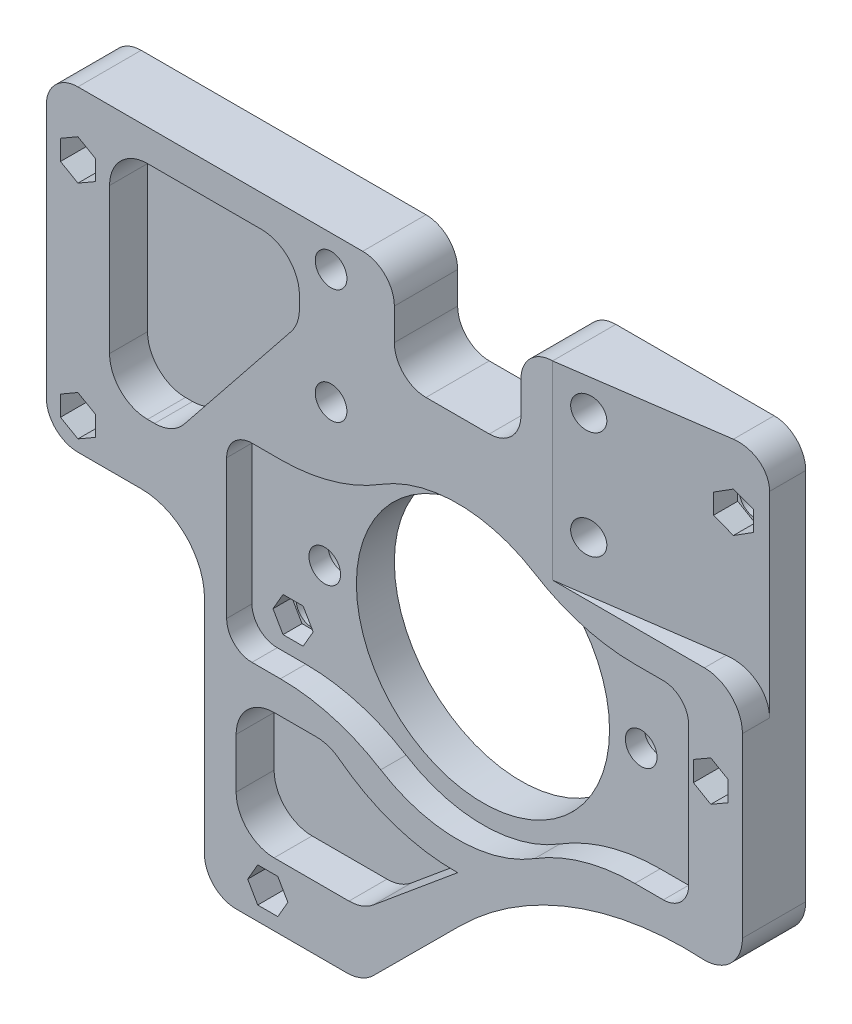
SolidWorks part; units mm, degrees
ref_plane "Front Plane" through (0, 0, 0) normal (0, 0, 1) x (1, 0, 0)
ref_plane "Top Plane" through (0, 0, 0) normal (0, 1, 0) x (1, 0, 0)
ref_plane "Right Plane" through (0, 0, 0) normal (1, 0, 0) x (0, 0, -1)
sketch "Sketch1" plane through (0, 0, 0) normal (0, 0, 1) x (1, 0, 0)
  line L0 (0, 5) -> (0, 40)
  line L1 (-10, 50) -> (-20, 50)
  line L2 (-25, 55) -> (-25, 95)
  line L3 (-20, 100) -> (25, 100)
  line L4 (30, 95) -> (30, 90)
  line L5 (35, 85) -> (45, 85)
  line L6 (50, 90) -> (50, 95)
  line L7 (55, 100) -> (80, 100)
  line L8 (85, 95) -> (85, 36)
  line L9 (5, 0) -> (22.471, 0)
  line L10 (26.706, 1.7498) -> (40.36, 15.355)
  line L11 (60, 95) -> (60, 77.99) construction
  line L12 (20, 95) -> (20, 76.86) construction
  arc A0 (85, 36) -> (79, 30) centre (79, 36) cw
  arc A1 (79, 30) -> (40.36, 15.355) centre (76.0188, -20.4315) ccw
  arc A2 (22.471, 0) -> (26.706, 1.7498) centre (22.471, 6) ccw
  arc A3 (0, 5) -> (5, 0) centre (5, 5) ccw
  arc A4 (0, 40) -> (-10, 50) centre (-10, 40) ccw
  arc A5 (-20, 50) -> (-25, 55) centre (-20, 55) cw
  arc A6 (80, 100) -> (85, 95) centre (80, 95) cw
  arc A7 (50, 95) -> (55, 100) centre (55, 95) cw
  arc A8 (45, 85) -> (50, 90) centre (45, 90) ccw
  arc A9 (30, 90) -> (35, 85) centre (35, 90) ccw
  arc A10 (25, 100) -> (30, 95) centre (25, 95) cw
  arc A11 (-25, 95) -> (-20, 100) centre (-20, 95) cw
  circle A12 centre (40, 50) radius 20
  circle A13 centre (10, 5) radius 2.5
  circle A14 centre (10, 40) radius 2.5
  circle A15 centre (15, 50) radius 2.5
  circle A16 centre (-20, 55) radius 2.5
  circle A17 centre (-20, 90) radius 2.5
  circle A18 centre (20, 95) radius 2.5
  circle A19 centre (20, 76.86) radius 2.5
  circle A20 centre (60, 77.99) radius 2.5
  circle A21 centre (60, 95) radius 2.5
  circle A22 centre (80, 90) radius 2.5
  circle A23 centre (80, 55) radius 2.5
  circle A24 centre (65, 50) radius 2.5
  point P18 (24.95, 0)
  point P21 (0, 0)
  point P24 (0, 50)
  point P27 (-25, 50)
  point P30 (85, 100)
  point P33 (50, 100)
  point P36 (50, 85)
  point P39 (30, 85)
  point P42 (30, 100)
  point P45 (-25, 100)
  dimension "D10" = 6
  dimension "D15" = 6
  dimension "D16" = 5
  dimension "D17" = 10
  dimension "D18" = 5
  dimension "D19" = 5
  dimension "D20" = 40
  dimension "D23" = 5
  dimension "D26" = 5
  dimension "D27" = 5
  dimension "D28" = 5
  dimension "D29" = 5
  dimension "D30" = 5
  dimension "D31" = 5
  dimension "D32" = 5
  dimension "D33" = 5
  dimension "D34" = 5
  dimension "D35" = 5
  dimension "D36" = 5
  dimension "D1" = 50
  dimension "D2" = 25
  dimension "D3" = 50
  dimension "D4" = 55
  dimension "D5" = 15
  dimension "D6" = 20
  dimension "D7" = 35
  dimension "D8" = 15
  dimension "D9" = 64
  dimension "D11" = 6
  dimension "D12" = 24.95
  dimension "D13" = 15.355
  dimension "D14" = 15.41
  dimension "D21" = 45
  dimension "D22" = 50
  dimension "D24" = 5
  dimension "D25" = 10
  dimension "D37" = 40
  dimension "D38" = 10
  dimension "D39" = 50
  dimension "D40" = 15
  dimension "D41" = 5
  dimension "D42" = 5
  dimension "D43" = 10
  dimension "D44" = 5
  dimension "D45" = 10
  dimension "D46" = 5
  dimension "D47" = 10
  dimension "D48" = 5
  dimension "D49" = 17.01
  dimension "D50" = 18.14
  dimension "D51" = 5
  dimension "D52" = 10
  dimension "D53" = 5
  dimension "D54" = 45
  dimension "D55" = 20
  dimension "D56" = 50
extrude "Boss-Extrude1" add sketch "Sketch1" along normal blind 10
sketch "Sketch2" plane through (0, 100, 0) normal (0, 1, 0) x (1, 0, 0)
  line L0 (55, -10) -> (85, -5.7143)
  line L1 (80, -10) -> (55, -10) construction
  line L2 (85, -10) -> (85, 0) construction
  line L3 (85, -5.7143) -> (85, -10)
  line L4 (85, -10) -> (55, -10)
  dimension "D1" = 30
  dimension "D2" = 4.2857
extrude "Cut-Extrude1" cut sketch "Sketch2" against normal blind 30
fillet "Fillet1" radius 6 1 edges at (85, 70, 7.8571)
sketch "Sketch3" plane through (0, 0, 10) normal (0, 0, 1) x (1, 0, 0)
  line L0 (76.5, 61) -> (76.5, 39)
  line L1 (72.5, 35) -> (68, 35)
  line L2 (3.5, 39) -> (3.5, 61)
  line L3 (7.5, 65) -> (12, 65)
  line L4 (85, 95) -> (85, 36) construction
  line L5 (79, 70) -> (55, 70) construction
  line L6 (12, 35) -> (7.5, 35)
  line L7 (68, 65) -> (72.5, 65)
  arc A0 (27.8491, 30.4717) -> (52.1509, 30.4717) centre (40, 50) ccw
  arc A1 (52.1509, 69.5283) -> (27.8491, 69.5283) centre (40, 50) ccw
  arc A2 (68, 35) -> (52.1509, 30.4717) centre (68, 5) ccw
  arc A3 (68, 65) -> (52.1509, 69.5283) centre (68, 95) cw
  arc A4 (12, 65) -> (27.8491, 69.5283) centre (12, 95) ccw
  arc A5 (12, 35) -> (27.8491, 30.4717) centre (12, 5) cw
  arc A6 (76.5, 39) -> (72.5, 35) centre (72.5, 39) cw
  arc A7 (76.5, 61) -> (72.5, 65) centre (72.5, 61) ccw
  arc A8 (3.5, 61) -> (7.5, 65) centre (7.5, 61) cw
  arc A9 (7.5, 35) -> (3.5, 39) centre (7.5, 39) cw
  point P18 (57.4356, 65)
  point P25 (76.5, 35)
  point P28 (76.5, 65)
  dimension "D5" = 46
  dimension "D6" = 30
  dimension "D7" = 4
  dimension "D1" = 8.5
  dimension "D2" = 30
  dimension "D3" = 5
  dimension "D4" = 73
extrude "Cut-Extrude2" cut sketch "Sketch3" against normal blind 4
sketch "Sketch4" plane through (0, 0, 10) normal (0, 0, 1) x (1, 0, 0)
  line L0 (-20, 100) -> (25, 100) construction
  line L1 (-25, 55) -> (-25, 95) construction
  line L2 (-9, 89) -> (-9, 66) construction
  line L3 (9, 89) -> (9, 67.0491) construction
  line L4 (-9, 66) -> (-7.8837, 66) construction
  line L5 (-15, 66) -> (-15, 89)
  line L6 (-9, 95) -> (9, 95)
  line L7 (-9, 60) -> (-7.8837, 60)
  line L8 (15, 89) -> (15, 87.1047)
  line L9 (-3.1985, 62.2518) -> (13.6852, 83.3565)
  line L10 (0, 5) -> (0, 40) construction
  line L11 (5, 0) -> (22.471, 0) construction
  line L12 (11, 23.8912) -> (17.6555, 23.8912) construction
  line L13 (5, 23.8912) -> (5, 16)
  line L14 (11, 10) -> (22.8317, 10)
  line L15 (11, 29.8912) -> (17.6555, 29.8912)
  line L16 (26.6674, 11.3861) -> (40, 22.47)
  arc A0 (-9, 95) -> (-15, 89) centre (-9, 89) ccw
  arc A1 (-7.8837, 60) -> (-3.1985, 62.2518) centre (-7.8837, 66) ccw
  arc A2 (-15, 66) -> (-9, 60) centre (-9, 66) ccw
  arc A3 (13.6852, 83.3565) -> (15, 87.1047) centre (9, 87.1047) ccw
  arc A4 (15, 89) -> (9, 95) centre (9, 89) ccw
  arc A5 (-8.4419, 71.974) -> (-9, 71.8953) centre (-7.8837, 66) ccw
  arc A6 (-8.4419, 71.974) -> (-9, 72) centre (-9, 66) ccw
  arc A7 (11, 29.8912) -> (5, 23.8912) centre (11, 23.8912) ccw
  arc A8 (5, 16) -> (11, 10) centre (11, 16) ccw
  arc A9 (22.8317, 10) -> (26.6674, 11.3861) centre (22.8317, 16) ccw
  arc A10 (21.3049, 28.6538) -> (40, 22.47) centre (39.5517, 52.4667) ccw
  arc A11 (21.3049, 28.6538) -> (17.6555, 29.8912) centre (17.6555, 23.8912) ccw
  dimension "D1" = 12
  dimension "D5" = 12
  dimension "D6" = 12
  dimension "D7" = 12
  dimension "D8" = 12
  dimension "D17" = 6
  dimension "D18" = 12
  dimension "D19" = 12
  dimension "D20" = 12
  dimension "D33" = 30
  dimension "D2" = 11
  dimension "D3" = 16
  dimension "D4" = 23
  dimension "D9" = 18
  dimension "D10" = 11
  dimension "D11" = 1.1162
  dimension "D12" = 1.8953
  dimension "D13" = 23
  dimension "D14" = 18
  dimension "D15" = 1.8953
  dimension "D16" = 1.1163
  dimension "D21" = 11
  dimension "D22" = 16
  dimension "D23" = 23.8912
  dimension "D24" = 11
  dimension "D25" = 16
  dimension "D26" = 22.8317
  dimension "D27" = 17.6555
  dimension "D28" = 40
  dimension "D29" = 22.47
  dimension "D30" = 6.6555
  dimension "D31" = 7.8912
  dimension "D32" = 11.8317
extrude "Cut-Extrude3" cut sketch "Sketch4" against normal blind 6
sketch "Sketch5" plane through (0, 0, 0) normal (0, 0, -1) x (-1, 0, 0)
  circle A0 centre (-65, 50) radius 3.75
  circle A1 centre (-15, 50) radius 3.75
  dimension "D1" = 7.5
  dimension "D2" = 7.5
extrude "Cut-Extrude4" cut sketch "Sketch5" against normal blind 3
sketch "Sketch6" plane through (0, 0, 0) normal (0, 0, -1) x (-1, 0, 0)
  line L1 (-56.8246, 95) -> (-58.4123, 97.75)
  line L2 (-58.4123, 97.75) -> (-61.5877, 97.75)
  line L3 (-61.5877, 97.75) -> (-63.1754, 95)
  line L4 (-63.1754, 95) -> (-61.5877, 92.25)
  line L5 (-61.5877, 92.25) -> (-58.4123, 92.25)
  line L6 (-58.4123, 92.25) -> (-56.8246, 95)
  line L7 (-56.8246, 77.99) -> (-58.4123, 80.74)
  line L8 (-58.4123, 80.74) -> (-61.5877, 80.74)
  line L9 (-61.5877, 80.74) -> (-63.1754, 77.99)
  line L10 (-63.1754, 77.99) -> (-61.5877, 75.24)
  line L11 (-61.5877, 75.24) -> (-58.4123, 75.24)
  line L12 (-58.4123, 75.24) -> (-56.8246, 77.99)
  line L13 (-16.8246, 76.86) -> (-18.4123, 79.61)
  line L14 (-18.4123, 79.61) -> (-21.5877, 79.61)
  line L15 (-21.5877, 79.61) -> (-23.1754, 76.86)
  line L16 (-23.1754, 76.86) -> (-21.5877, 74.11)
  line L17 (-21.5877, 74.11) -> (-18.4123, 74.11)
  line L18 (-18.4123, 74.11) -> (-16.8246, 76.86)
  line L19 (-16.8246, 95) -> (-18.4123, 97.75)
  line L20 (-18.4123, 97.75) -> (-21.5877, 97.75)
  line L21 (-21.5877, 97.75) -> (-23.1754, 95)
  line L22 (-23.1754, 95) -> (-21.5877, 92.25)
  line L23 (-21.5877, 92.25) -> (-18.4123, 92.25)
  line L24 (-18.4123, 92.25) -> (-16.8246, 95)
  circle A0 centre (-60, 95) radius 2.75 construction
  circle A1 centre (-60, 77.99) radius 2.75 construction
  circle A2 centre (-20, 76.86) radius 2.75 construction
  circle A3 centre (-20, 95) radius 2.75 construction
  dimension "D1" = 5.5
  dimension "D4" = 5.5
  dimension "D5" = 5.5
  dimension "D7" = 5.5
  dimension "D2" = 2.75
  dimension "D3" = 2.75
  dimension "D6" = 2.75
  dimension "D8" = 2.75
extrude "Cut-Extrude5" cut sketch "Sketch6" against normal blind 5
sketch "Sketch7" plane through (0, 0, 10) normal (0, 0, 1) x (1, 0, 0)
  line L1 (-17.25, 91.5877) -> (-20, 93.1754)
  line L2 (-20, 93.1754) -> (-22.75, 91.5877)
  line L3 (-22.75, 91.5877) -> (-22.75, 88.4123)
  line L4 (-22.75, 88.4123) -> (-20, 86.8246)
  line L5 (-20, 86.8246) -> (-17.25, 88.4123)
  line L6 (-17.25, 88.4123) -> (-17.25, 91.5877)
  line L7 (-17.25, 56.5877) -> (-20, 58.1754)
  line L8 (-20, 58.1754) -> (-22.75, 56.5877)
  line L9 (-22.75, 56.5877) -> (-22.75, 53.4123)
  line L10 (-22.75, 53.4123) -> (-20, 51.8246)
  line L11 (-20, 51.8246) -> (-17.25, 53.4123)
  line L12 (-17.25, 53.4123) -> (-17.25, 56.5877)
  line L13 (82.75, 91.5877) -> (80, 93.1754)
  line L14 (80, 93.1754) -> (77.25, 91.5877)
  line L15 (77.25, 91.5877) -> (77.25, 88.4123)
  line L16 (77.25, 88.4123) -> (80, 86.8246)
  line L17 (80, 86.8246) -> (82.75, 88.4123)
  line L18 (82.75, 88.4123) -> (82.75, 91.5877)
  line L19 (82.75, 56.5877) -> (80, 58.1754)
  line L20 (80, 58.1754) -> (77.25, 56.5877)
  line L21 (77.25, 56.5877) -> (77.25, 53.4123)
  line L22 (77.25, 53.4123) -> (80, 51.8246)
  line L23 (80, 51.8246) -> (82.75, 53.4123)
  line L24 (82.75, 53.4123) -> (82.75, 56.5877)
  line L25 (13.1754, 40) -> (11.5877, 42.75)
  line L26 (11.5877, 42.75) -> (8.4123, 42.75)
  line L27 (8.4123, 42.75) -> (6.8246, 40)
  line L28 (6.8246, 40) -> (8.4123, 37.25)
  line L29 (8.4123, 37.25) -> (11.5877, 37.25)
  line L30 (11.5877, 37.25) -> (13.1754, 40)
  line L31 (13.1754, 5) -> (11.5877, 7.75)
  line L32 (11.5877, 7.75) -> (8.4123, 7.75)
  line L33 (8.4123, 7.75) -> (6.8246, 5)
  line L34 (6.8246, 5) -> (8.4123, 2.25)
  line L35 (8.4123, 2.25) -> (11.5877, 2.25)
  line L36 (11.5877, 2.25) -> (13.1754, 5)
  circle A0 centre (-20, 90) radius 2.75 construction
  circle A1 centre (-20, 55) radius 2.75 construction
  circle A2 centre (80, 90) radius 2.75 construction
  circle A3 centre (80, 55) radius 2.75 construction
  circle A4 centre (10, 40) radius 2.75 construction
  circle A5 centre (10, 5) radius 2.75 construction
  dimension "D1" = 5.5
  dimension "D3" = 5.5
  dimension "D5" = 5.5
  dimension "D7" = 5.5
  dimension "D9" = 5.5
  dimension "D11" = 5.5
  dimension "D2" = 1.5877
  dimension "D4" = 1.5877
  dimension "D6" = 2.75
  dimension "D8" = 2.75
  dimension "D10" = 1.5877
  dimension "D12" = 1.5877
extrude "Cut-Extrude6" cut sketch "Sketch7" against normal blind 7
